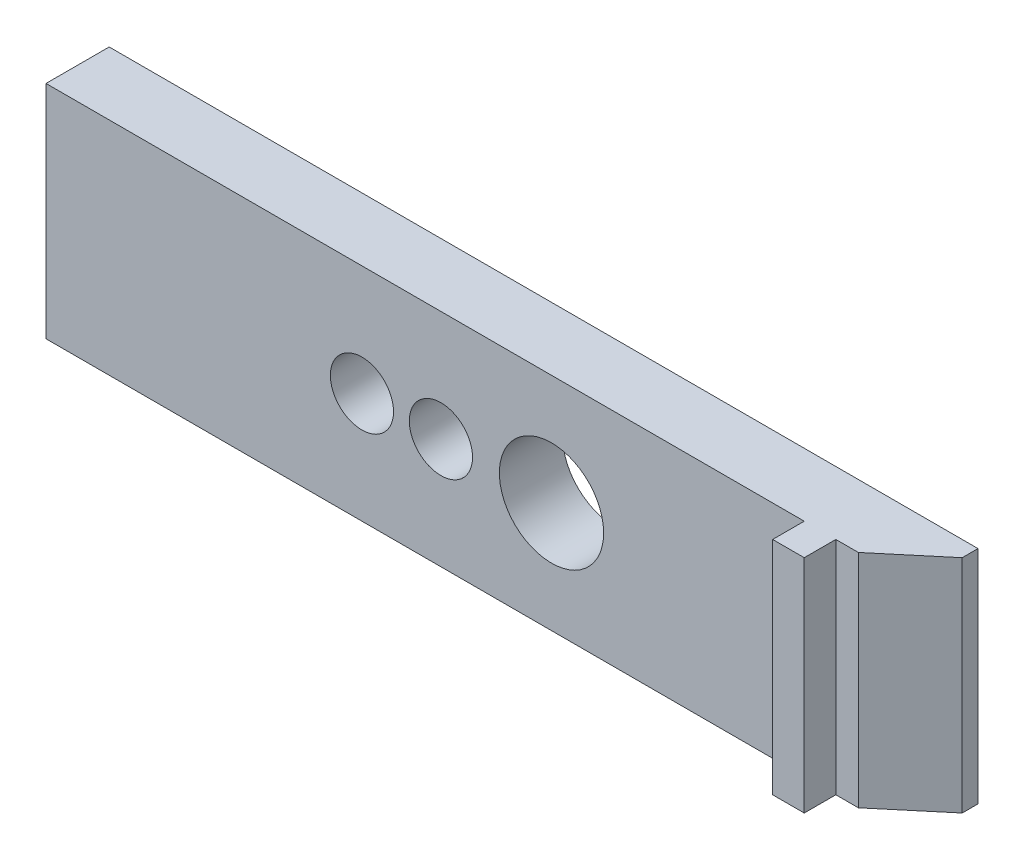
SolidWorks part; units mm, degrees
ref_plane "Plano frontal" through (0, 0, 0) normal (0, 0, 1) x (1, 0, 0)
ref_plane "Plano superior" through (0, 0, 0) normal (0, 1, 0) x (1, 0, 0)
ref_plane "Plano direito" through (0, 0, 0) normal (1, 0, 0) x (0, 0, -1)
sketch "Esboço1" plane through (0, 0, 0) normal (0, 0, 1) x (1, 0, 0)
  line L1 (-13.75, 3.5) -> (13.75, 3.5)
  line L2 (-13.75, 3.5) -> (-13.75, -3.5)
  line L3 (-13.75, -3.5) -> (13.75, -3.5)
  line L4 (13.75, 3.5) -> (13.75, -3.5)
  line L5 (-13.75, 3.5) -> (13.75, -3.5) construction
  line L6 (-13.75, -3.5) -> (13.75, 3.5) construction
  circle A0 centre (2.25, 0) radius 1.65
  circle A1 centre (-1.25, 0) radius 1
  circle A2 centre (-3.75, 0) radius 1
  point P0 (0, 0)
  point P12 (0.4778, 0)
  point P13 (0, 0)
  dimension "D4" = 2
  dimension "D5" = 3.3
  dimension "D1" = 16
  dimension "D2" = 3.5
  dimension "D3" = 2.5
  dimension "D6" = 3.5
  dimension "D7" = 27.5
extrude "Ressalto-extrusão1" add sketch "Esboço1" along normal blind 2
chamfer "Chanfro1" distance 1.5 angle 50 1 edges at (13.75, 0, 2)
sketch "Esboço2" plane through (0, 0, 2) normal (0, 0, 1) x (1, 0, 0)
  line L0 (11.9624, 3.5) -> (-13.75, 3.5) construction
  line L1 (11.25, -3.5) -> (10.25, -3.5)
  line L2 (11.25, -3.5) -> (11.25, 3.5)
  line L3 (11.25, 3.5) -> (10.25, 3.5)
  line L4 (10.25, -3.5) -> (10.25, 3.5)
  line L5 (11.25, -3.5) -> (10.25, 3.5) construction
  line L6 (11.25, 3.5) -> (10.25, -3.5) construction
  line L7 (-13.75, 3.5) -> (-13.75, -3.5) construction
  line L8 (-13.75, -3.5) -> (11.9624, -3.5) construction
  point P0 (10.75, 0)
  point P10 (0, 0)
  point P11 (11.5, -3.5)
  point P12 (0, 0)
  dimension "D1" = 1
  dimension "D2" = 25
extrude "Ressalto-extrusão2" add sketch "Esboço2" along normal blind 1
